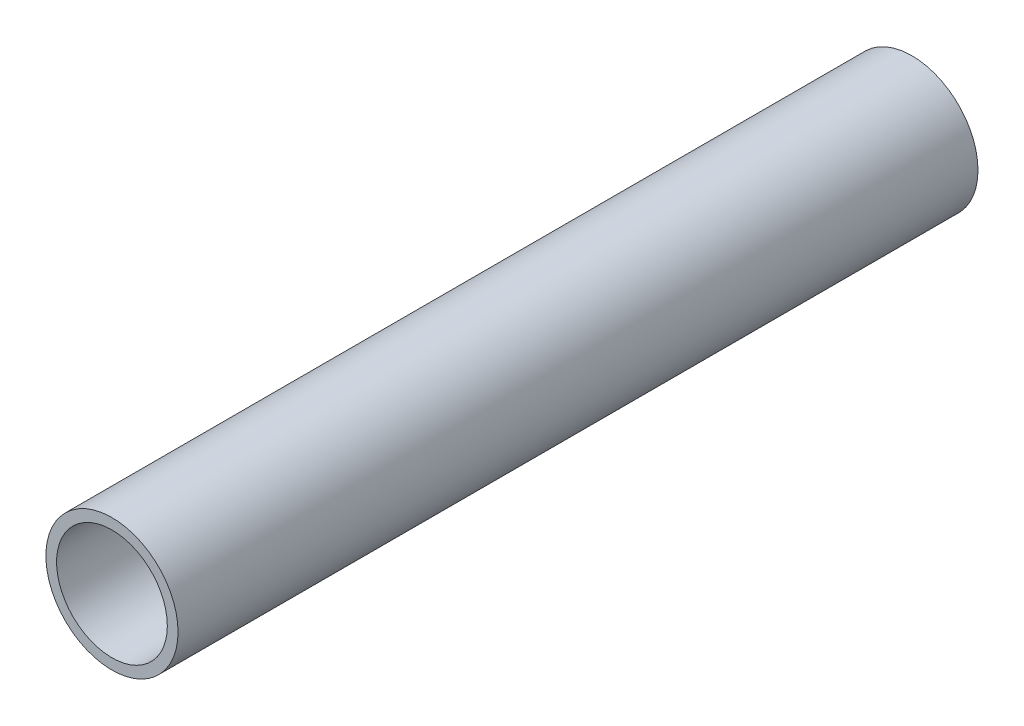
SolidWorks part; units mm, degrees
material "PVC Rigid"
ref_plane "Front Plane" through (0, 0, 0) normal (0, 0, 1) x (1, 0, 0)
ref_plane "Top Plane" through (0, 0, 0) normal (0, 1, 0) x (1, 0, 0)
ref_plane "Right Plane" through (0, 0, 0) normal (1, 0, 0) x (0, 0, -1)
sketch "Sketch1" plane through (0, 0, 0) normal (0, 0, 1) x (1, 0, 0)
  circle A0 centre (-325.6373, 52.475) radius 24.13
  circle A1 centre (-325.6373, 52.475) radius 20.2184
  dimension "D1" = 48.26
  dimension "D2" = 3.9116
extrude "Boss-Extrude1" add sketch "Sketch1" against normal blind 292.1
ref_plane "Plane1" through (0, 28.345, 0) normal (0, -1, 0) x (-1, 0, 0)
hole_wizard "1/4 (0.25) Diameter Hole1" positions "Sketch2" profile "Sketch3" hole size "1/4" standard "ANSI Inch"
sketch "Sketch2" plane through (0, 28.345, 0) normal (0, -1, 0) x (-1, 0, 0)
  circle A0 centre (325.6373, 50.8) radius 2.4574 construction
  circle A1 centre (325.6373, 241.3) radius 2.4574 construction
  point P0 (325.6373, 50.8)
  point P2 (325.6373, 241.3)
sketch "Sketch3" plane through (-325.6373, 28.345, -50.8) normal (1, 0, 0) x (0, 0, -1)
  line L0 (0, 0) -> (0, 3.9116)
  line L1 (0, 3.9116) -> (3.175, 3.9116)
  line L2 (3.175, 3.9116) -> (3.175, 0)
  line L5 (3.175, 0) -> (0, 0)
  line L11 (0, -6.35) -> (0, 107.95) construction
  dimension "Thru Hole Dia." = 6.35
  dimension "Thru Hole Depth" = 3.9116
